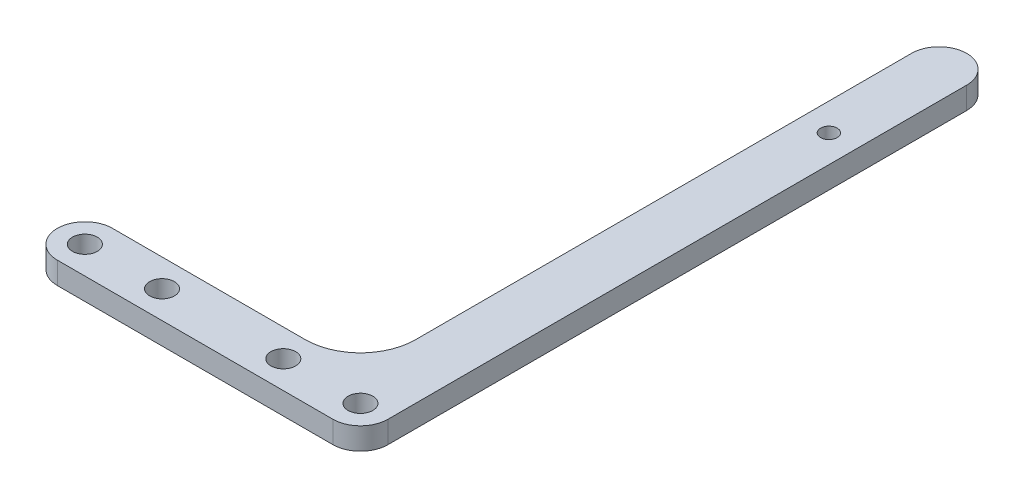
SolidWorks part; units mm, degrees
ref_plane "Front" through (0, 0, 0) normal (0, 0, 1) x (1, 0, 0)
ref_plane "Top" through (0, 0, 0) normal (0, 1, 0) x (1, 0, 0)
ref_plane "Right" through (0, 0, 0) normal (1, 0, 0) x (0, 0, -1)
sketch "Sketch1" plane through (0, 0, 0) normal (0, 1, 0) x (1, 0, 0)
  line L0 (0, 0) -> (0, 100)
  line L2 (10, 100) -> (10, 0)
  line L3 (10, 0) -> (0, 0)
  circle A0 centre (5, 80) radius 1.5
  arc A2 (10, 100) -> (0, 100) centre (5, 100) ccw
  dimension "D1" = 3
  dimension "D2" = 80
  dimension "D3" = 10
  dimension "D4" = 20
extrude "Boss-Extrude1" add sketch "Sketch1" along normal blind 4
sketch "Sketch2" plane through (0, 4, 0) normal (0, 1, 0) x (1, 0, 0)
  line L0 (0, 0) -> (-45, 0)
  line L1 (-45, -10) -> (10, -10)
  line L2 (10, 0) -> (10, 100) construction
  line L3 (0, 0) -> (0, -10) construction
  line L4 (0, -5) -> (-45, -5) construction
  line L5 (10, -10) -> (10, 0)
  arc A0 (-45, 0) -> (-45, -10) centre (-45, -5) ccw
  circle A1 centre (-45, -5) radius 2.25
  circle A2 centre (-31, -5) radius 2.25
  circle A3 centre (-9, -5) radius 2.25
  circle A4 centre (5, -5) radius 2.25
  dimension "D2" = 4.5
  dimension "D3" = 4.5
  dimension "D4" = 4.5
  dimension "D5" = 4.5
  dimension "D1" = 10
  dimension "D6" = 14
  dimension "D7" = 14
  dimension "D8" = 5
  dimension "D9" = 50
extrude "Boss-Extrude2" add sketch "Sketch2" against normal blind 4
fillet "Fillet1" radius 10 1 edges at (0, 2, 0)
sketch "Sketch3" [suppressed] plane through (0, 4, 0) normal (0, 1, 0) x (1, 0, 0)
  line L0 (10, -17.9129) -> (10, 30)
  line L4 (0, 30) -> (10, 30)
  line L5 (10, 30) -> (10, 100)
  line L6 (0, 100) -> (0, 30)
  line L8 (10, 30) -> (10, 100)
  line L9 (0, 100) -> (0, 30)
  arc A0 (0, 30) -> (10, -17.9129) centre (0, 5) ccw
  circle A1 centre (0, 5) radius 2.5
  arc A2 (10, 100) -> (0, 100) centre (5, 100) ccw
  arc A3 (10, 100) -> (0, 100) centre (5, 100) ccw
  dimension "D1" = 0
  dimension "D4" = 5
  dimension "D3" = 25
extrude "Boss-Extrude3" [suppressed] add sketch "Sketch3" against normal blind 4
fillet "Fillet2" radius 5 1 edges at (10, 2, 10)
equation "\"D3@Sketch2\"=\"D2@Sketch2\""
equation "\"D4@Sketch2\"=\"D2@Sketch2\""
equation "\"D5@Sketch2\"=\"D2@Sketch2\""
equation "\"D7@Sketch2\"=\"D6@Sketch2\""
equation "\"D8@Sketch2\"=\"D1@Sketch2\"/2"
